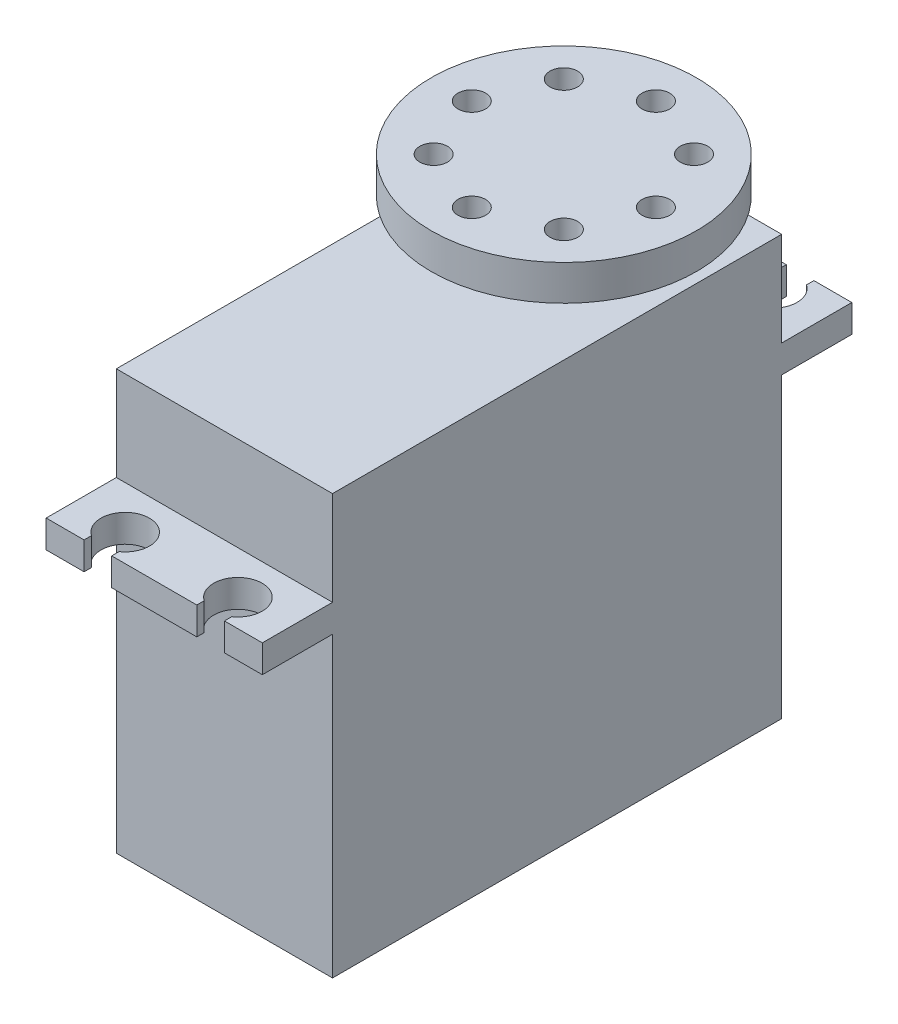
SolidWorks part; units mm, degrees
ref_plane "Front Plane" through (0, 0, 0) normal (0, 0, 1) x (1, 0, 0)
ref_plane "Top Plane" through (0, 0, 0) normal (0, 1, 0) x (1, 0, 0)
ref_plane "Right Plane" through (0, 0, 0) normal (1, 0, 0) x (0, 0, -1)
sketch "Sketch1" plane through (0, 0, 0) normal (0, 1, 0) x (1, 0, 0)
  line L0 (-9.78, -20.32) -> (9.78, -20.32)
  line L1 (-9.78, -20.32) -> (-9.78, 20.32)
  line L2 (9.78, -20.32) -> (9.78, 20.32)
  line L3 (-9.78, 20.32) -> (9.78, 20.32)
  line L4 (-9.78, -20.32) -> (9.78, 20.32) construction
  line L5 (9.78, -20.32) -> (-9.78, 20.32) construction
  point P1 (0, 0)
  dimension "D1" = 19.56
  dimension "D2" = 40.64
extrude "Boss-Extrude1" add sketch "Sketch1" along normal blind 37.96
sketch "Sketch2" plane through (9.78, 0, 0) normal (1, 0, 0) x (0, 0, -1)
  line L0 (0, 37.96) -> (0, 0) construction
  line L1 (-26.67, 29.44) -> (26.67, 29.44)
  line L2 (-26.67, 29.44) -> (-26.67, 26.94)
  line L3 (-26.67, 26.94) -> (26.67, 26.94)
  line L4 (26.67, 29.44) -> (26.67, 26.94)
  line L5 (-20.32, 37.96) -> (20.32, 37.96) construction
  line L6 (-20.32, 0) -> (20.32, 0) construction
  dimension "D1" = 26.94
  dimension "D2" = 29.44
  dimension "D3" = 53.34
extrude "Boss-Extrude2" add sketch "Sketch2" against normal up to surface (19.56 mm away) up to face at (-9.78, 18.98, 0)
sketch "Sketch3" plane through (0, 29.44, 0) normal (0, 1, 0) x (1, 0, 0)
  line L0 (0, 26.67) -> (0, -26.67) construction
  line L1 (-9.78, 26.67) -> (9.78, 26.67) construction
  line L2 (-9.78, -26.67) -> (9.78, -26.67) construction
  line L3 (0, 0) -> (-24.491, 0) construction
  circle A0 centre (-5.1, 24.2) radius 2.195
  circle A1 centre (5.1, 24.2) radius 2.195
  circle A2 centre (5.1, -24.2) radius 2.195
  circle A3 centre (-5.1, -24.2) radius 2.195
  dimension "D1" = 4.39
  dimension "D2" = 10.2
  dimension "D3" = 48.4
extrude "Cut-Extrude1" cut sketch "Sketch3" against normal through all
sketch "Sketch4" plane through (0, 29.44, 0) normal (0, 1, 0) x (1, 0, 0)
  line L0 (0, 26.67) -> (0, 0) construction
  line L1 (-9.78, 26.67) -> (9.78, 26.67) construction
  line L2 (0, 0) -> (-18.7354, 0) construction
  line L3 (3.85, 26.67) -> (3.85, 26.0043)
  line L4 (-6.35, 26.67) -> (-3.85, 26.67)
  line L5 (-6.35, 26.67) -> (-6.35, 26.0043)
  line L6 (-6.35, 26.0043) -> (-3.85, 26.0043)
  line L7 (-3.85, 26.67) -> (-3.85, 26.0043)
  line L8 (6.35, 26.0043) -> (3.85, 26.0043)
  line L9 (6.35, 26.67) -> (6.35, 26.0043)
  line L10 (6.35, 26.67) -> (3.85, 26.67)
  line L11 (6.35, -26.67) -> (3.85, -26.67)
  line L12 (6.35, -26.67) -> (6.35, -26.0043)
  line L13 (6.35, -26.0043) -> (3.85, -26.0043)
  line L14 (-3.85, -26.67) -> (-3.85, -26.0043)
  line L15 (-6.35, -26.0043) -> (-3.85, -26.0043)
  line L16 (-6.35, -26.67) -> (-6.35, -26.0043)
  line L17 (-6.35, -26.67) -> (-3.85, -26.67)
  line L18 (3.85, -26.67) -> (3.85, -26.0043)
  circle A0 centre (-5.1, 24.2) radius 2.195 construction
  dimension "D1" = 2.5
extrude "Cut-Extrude2" cut sketch "Sketch4" against normal through all
sketch "Sketch5" plane through (0, 37.96, 0) normal (0, 1, 0) x (1, 0, 0)
  line L0 (-5.1, 24.2) -> (5.1, 24.2) construction
  line L1 (0, 24.2) -> (0, 0) construction
  arc A0 (-6.35, 26.0043) -> (-3.85, 26.0043) centre (-5.1, 24.2) ccw construction
  arc A1 (3.85, 26.0043) -> (6.35, 26.0043) centre (5.1, 24.2) ccw construction
  arc A2 (-6.35, 26.0043) -> (-3.85, 26.0043) centre (-5.1, 24.2) ccw construction
  arc A3 (3.85, 26.0043) -> (6.35, 26.0043) centre (5.1, 24.2) ccw construction
  circle A4 centre (0, 10.39) radius 6
  dimension "D1" = 12
  dimension "D2" = 13.81
extrude "Boss-Extrude3" add sketch "Sketch5" along normal blind 3.15
sketch "Sketch6" plane through (0, 41.11, 0) normal (0, 1, 0) x (1, 0, 0)
  circle A0 centre (0, 10.39) radius 12
  dimension "D1" = 24
extrude "Boss-Extrude4" add sketch "Sketch6" along normal blind 3.2
sketch "Sketch7" plane through (0, 44.31, 0) normal (0, 1, 0) x (1, 0, 0)
  line L0 (0, 22.39) -> (0, 10.39) construction
  circle A0 centre (0, 10.39) radius 12 construction
  circle A1 centre (0, 18.72) radius 1.25
  circle A2 centre (5.8902, 16.2802) radius 1.25
  circle A3 centre (8.33, 10.39) radius 1.25
  circle A4 centre (5.8902, 4.4998) radius 1.25
  circle A5 centre (0, 2.06) radius 1.25
  circle A6 centre (-5.8902, 4.4998) radius 1.25
  circle A7 centre (-8.33, 10.39) radius 1.25
  circle A8 centre (-5.8902, 16.2802) radius 1.25
  point P0 (0, 10.39)
  point P24 (0, 10.39)
  dimension "D1" = 2.5
  dimension "D2" = 8.33
  dimension "D3" = 8
extrude "Cut-Extrude3" cut sketch "Sketch7" against normal up to surface (3.2 mm away) up to face at (0, 41.11, 1.61)
sketch "Sketch8" plane through (0, 0, 0) normal (0, -1, 0) x (1, 0, 0)
  circle A0 centre (0, -10.39) radius 6 construction
  circle A1 centre (0, -10.39) radius 6 construction
  circle A2 centre (0, -10.39) radius 3.685
  dimension "D1" = 7.37
extrude "Boss-Extrude5" add sketch "Sketch8" along normal blind 4.06
